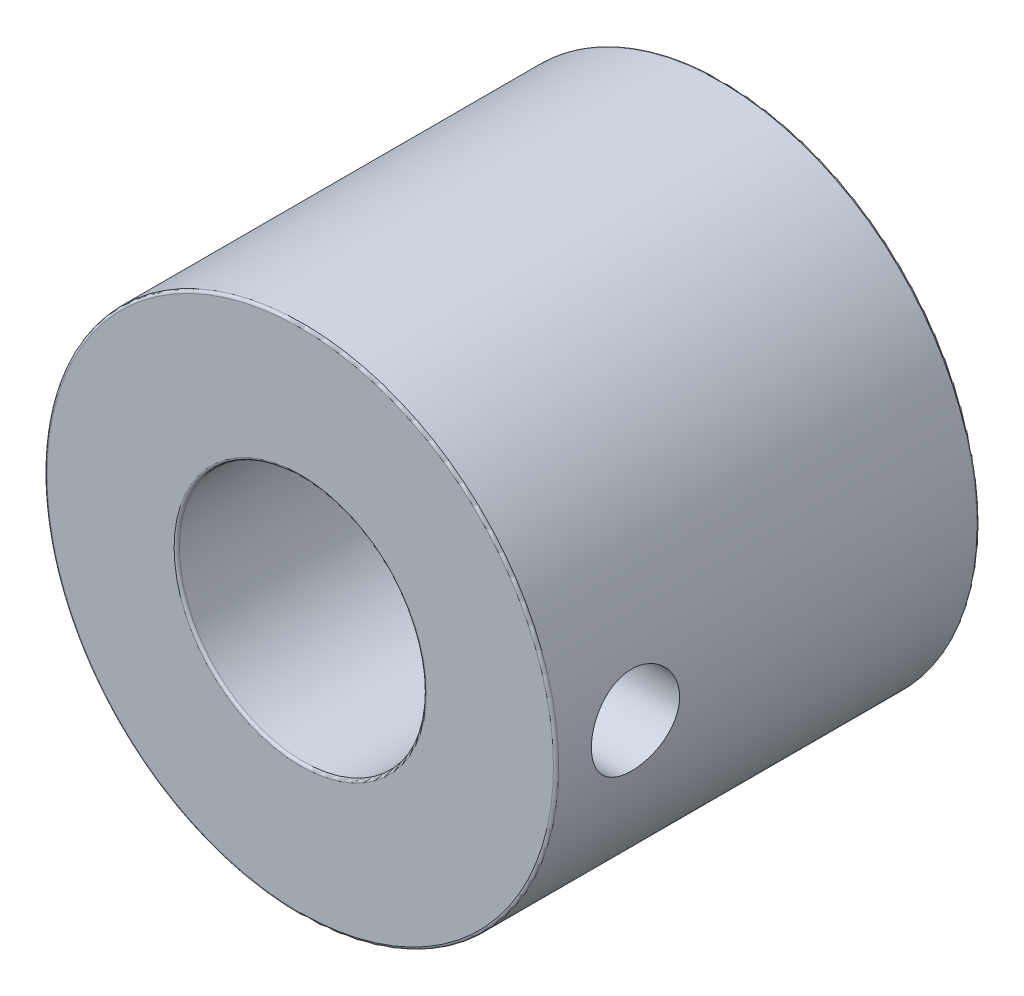
SolidWorks part; units mm, degrees
ref_plane "Front Plane" through (0, 0, 0) normal (0, 0, 1) x (1, 0, 0)
ref_plane "Top Plane" through (0, 0, 0) normal (0, 1, 0) x (1, 0, 0)
ref_plane "Right Plane" through (0, 0, 0) normal (1, 0, 0) x (0, 0, -1)
sketch "Sketch4" plane through (0, 0, 0) normal (0, 0, 1) x (1, 0, 0)
  circle A0 centre (0, 0) radius 29
  dimension "D1" = 58
extrude "Boss-Extrude1" add sketch "Sketch4" along normal blind 48
sketch "Sketch5" plane through (0, 0, 0) normal (0, 0, -1) x (-1, 0, 0)
  circle A0 centre (0, 0) radius 24
  dimension "D1" = 48
extrude "Cut-Extrude1" cut sketch "Sketch5" against normal blind 25
sketch "Sketch6" plane through (0, 0, 48) normal (0, 0, 1) x (1, 0, 0)
  circle A0 centre (0, 0) radius 14
  dimension "D1" = 28
extrude "Cut-Extrude2" cut sketch "Sketch6" against normal through all and the other way through all
sketch "Sketch7" plane through (0, 0, 0) normal (1, 0, 0) x (0, 0, -1)
  line L0 (-48, 14) -> (-48, -14) construction
  circle A0 centre (-39, 0) radius 5
  point P4 (0, 0)
  dimension "D2" = 10
  dimension "D1" = 9
extrude "Cut-Extrude3" cut sketch "Sketch7" along normal blind 42 contours A0
fillet "Fillet1" radius 0.3 4 edges at (-14, 0, 25) (14, 0, 48) (29, 0, 0) (29, 0, 48)
